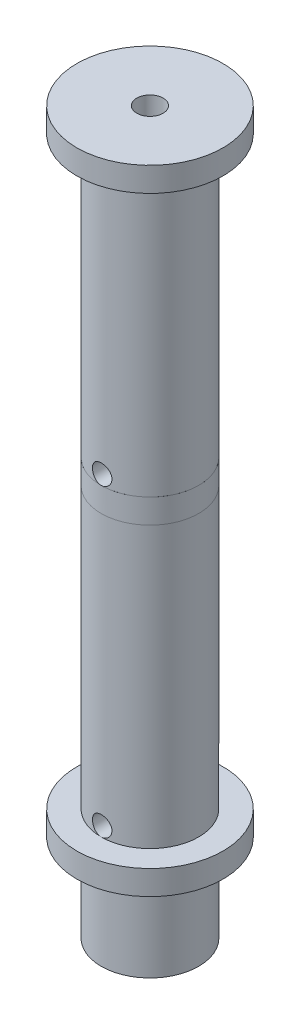
SolidWorks part; units mm, degrees
material "ABS"
ref_plane "Front Plane" through (0, 0, 0) normal (0, 0, 1) x (1, 0, 0)
ref_plane "Top Plane" through (0, 0, 0) normal (0, 1, 0) x (1, 0, 0)
ref_plane "Right Plane" through (0, 0, 0) normal (1, 0, 0) x (0, 0, -1)
sketch "Sketch1" plane through (0, 0, 0) normal (0, 1, 0) x (1, 0, 0)
  line L1 (3.5855, -6.0628) -> (7.0433, 0.0738)
  line L2 (7.0433, 0.0738) -> (3.4578, 6.1365)
  line L3 (3.4578, 6.1365) -> (-3.5855, 6.0628)
  line L4 (-3.5855, 6.0628) -> (-7.0433, -0.0738)
  line L5 (-7.0433, -0.0738) -> (-3.4578, -6.1365)
  line L6 (-3.4578, -6.1365) -> (3.5855, -6.0628)
  circle A0 centre (0, 0) radius 6.1 construction
  circle A1 centre (0, 0) radius 10
  dimension "D2" = 20
  dimension "D1" = 12.2
extrude "Boss-Extrude1" add sketch "Sketch1" along normal blind 18 contours A1 L6 L5 L4 L3 L2 L1
sketch "Sketch2" plane through (0, 18, 0) normal (0, 1, 0) x (1, 0, 0)
  circle A0 centre (0, 0) radius 15
  dimension "D1" = 30
extrude "Boss-Extrude2" add sketch "Sketch2" along normal blind 5
sketch "Sketch3" plane through (-5.3144, 0, -2.9945) normal (0.8712, 0, 0.4909) x (0.4909, 0, -0.8712)
  line L0 (-3.5218, 18) -> (3.5218, 18) construction
  line L1 (0, 18) -> (0, -0.0617) construction
  circle A0 centre (0, 5) radius 1.75
  dimension "D1" = 3.5
  dimension "D2" = 13
extrude "Cut-Extrude1" cut sketch "Sketch3" against normal blind 120
sketch "Sketch4" plane through (0, 23, 0) normal (0, 1, 0) x (1, 0, 0)
  circle A0 centre (0, 0) radius 10
  dimension "D1" = 20
extrude "Boss-Extrude3" add sketch "Sketch4" along normal blind 120
sketch "Sketch6" plane through (0, 143, 0) normal (0, 1, 0) x (1, 0, 0)
  circle A0 centre (0, 0) radius 5
  dimension "D1" = 10
extrude "Cut-Extrude3" cut sketch "Sketch6" against normal up to surface (120 mm away) contours A0 up to face at (0, 23, 10)
sketch "Sketch5" plane through (0, 143, 0) normal (0, 1, 0) x (1, 0, 0)
  circle A0 centre (0, 0) radius 15
  dimension "D1" = 30
extrude "Boss-Extrude4" add sketch "Sketch5" along normal blind 5
sketch "Sketch7" plane through (0, 148, 0) normal (0, 1, 0) x (1, 0, 0)
  circle A0 centre (0, 0) radius 2.7
  dimension "D1" = 5.4
extrude "Cut-Extrude4" cut sketch "Sketch7" against normal through all
ref_plane "Plane1" through (0, 83, 0) normal (0, 1, 0) x (1, 0, 0)
sketch "Sketch9" plane through (0, 83, 0) normal (0, 1, 0) x (1, 0, 0)
  circle A0 centre (0, 0) radius 10.005
  dimension "D1" = 20.01
extrude "Boss-Extrude5" add sketch "Sketch9" along normal blind 2.5 and the other way blind 2.5 contours A0
sketch "Sketch10" plane through (0, 0, 0) normal (0, 0, 1) x (1, 0, 0)
  line L0 (0, 148) -> (0, 23) construction
  line L1 (2.7, 148) -> (-2.7, 148) construction
  line L2 (15, 23) -> (-15, 23) construction
  line L3 (10.005, 85.5) -> (-10.005, 85.5) construction
  circle A0 centre (0, 25) radius 2
  circle A1 centre (0, 87.5) radius 2
  dimension "D1" = 4
  dimension "D2" = 4
extrude "Cut-Extrude5" cut sketch "Sketch10" against normal through all and the other way through all
sketch "Sketch11" plane through (0, 0, 0) normal (0, 0, 1) x (1, 0, 0)
  line L0 (0, 0) -> (0, 148) construction
  line L1 (15, 148) -> (-15, 148) construction
